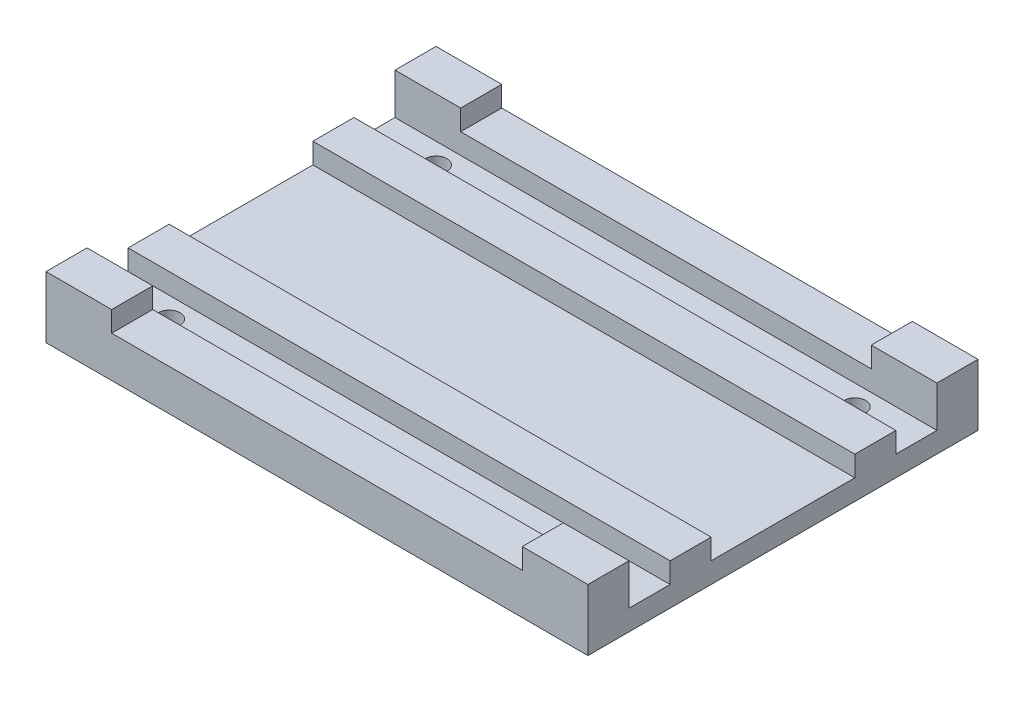
SolidWorks part; units mm, degrees
material "ABS"
ref_plane "Front Plane" through (0, 0, 0) normal (0, 0, 1) x (1, 0, 0)
ref_plane "Top Plane" through (0, 0, 0) normal (0, 1, 0) x (1, 0, 0)
ref_plane "Right Plane" through (0, 0, 0) normal (1, 0, 0) x (0, 0, -1)
sketch "Sketch1" plane through (0, 0, 0) normal (0, 1, 0) x (1, 0, 0)
  line L0 (-66, -47.5) -> (66, -47.5)
  line L1 (-66, -47.5) -> (-66, 47.5)
  line L2 (66, -47.5) -> (66, 47.5)
  line L3 (-66, 47.5) -> (66, 47.5)
  line L4 (-66, -47.5) -> (66, 47.5) construction
  line L5 (66, -47.5) -> (-66, 47.5) construction
  point P1 (0, 0)
  dimension "D1" = 95
  dimension "D2" = 132
extrude "Boss-Extrude1" add sketch "Sketch1" along normal blind 5
hole_wizard "M5 Clearance Slot1" positions "Sketch3" profile "Sketch2" size "M5" standard "ANSI Metric" slot yes end condition through all
sketch "Sketch3" plane through (0, 5, 0) normal (0, 1, 0) x (1, 0, 0)
  line L0 (-66, 47.5) -> (-66, -47.5) construction
  line L1 (66, 47.5) -> (-66, 47.5) construction
  line L2 (-51, 32.5) -> (51, 32.5) construction
  line L3 (51, 32.5) -> (51, -32.5) construction
  line L4 (51, -32.5) -> (-51, -32.5) construction
  line L5 (-51, -32.5) -> (-51, 32.5) construction
  line L7 (66, -47.5) -> (66, 47.5) construction
  line L8 (-66, -47.5) -> (66, -47.5) construction
  point P0 (-51, 32.5)
  point P2 (51, 32.5)
  point P4 (51, -32.5)
  point P6 (-51, -32.5)
  dimension "D1" = 15
  dimension "D2" = 15
  dimension "D3" = 15
  dimension "D4" = 15
sketch "Sketch2" plane through (-51, 5, -32.5) normal (1, 0, 0) x (0, 0, 1)
  line L0 (0, 0) -> (0, 5)
  line L1 (0, 5) -> (2.65, 5)
  line L2 (2.65, 5) -> (2.65, 0)
  line L5 (2.65, 0) -> (0, 0)
  line L11 (0, -6.35) -> (0, 107.95) construction
  dimension "Thru Hole Dia." = 5.3
  dimension "Thru Hole Depth" = 5
sketch "Sketch4" plane through (0, 5, 0) normal (0, 1, 0) x (1, 0, 0)
  line L0 (-66, 27.5) -> (-66, 17.5)
  line L1 (-66, 27.5) -> (66, 27.5)
  line L2 (-66, 17.5) -> (66, 17.5)
  line L3 (66, 27.5) -> (66, 17.5)
  line L4 (-66, 47.5) -> (-66, -47.5) construction
  line L5 (66, 37.5) -> (66, 47.5)
  line L6 (-66, 0) -> (66, 0) construction
  line L7 (66, -47.5) -> (66, 47.5) construction
  line L8 (-66, 32.5) -> (66, 32.5) construction
  line L9 (66, 47.5) -> (-66, 47.5) construction
  line L10 (-66, 47.5) -> (66, 47.5)
  line L11 (-66, 37.5) -> (-66, 47.5)
  line L12 (-66, 37.5) -> (66, 37.5)
  line L13 (-66, -27.5) -> (-66, -17.5)
  line L14 (66, -27.5) -> (66, -17.5)
  line L15 (-66, -17.5) -> (66, -17.5)
  line L16 (-66, -27.5) -> (66, -27.5)
  line L17 (66, -37.5) -> (66, -47.5)
  line L18 (-66, -37.5) -> (66, -37.5)
  line L19 (-66, -37.5) -> (-66, -47.5)
  line L20 (-66, -47.5) -> (66, -47.5)
  dimension "D1" = 15
  dimension "D2" = 10
  dimension "D3" = 5
extrude "Boss-Extrude2" add sketch "Sketch4" along normal blind 10
sketch "Sketch5" plane through (0, 15, 0) normal (0, 1, 0) x (1, 0, 0)
  line L0 (66, 27.5) -> (-66, 27.5) construction
  line L1 (-50, -50) -> (50, -50)
  line L2 (-50, -50) -> (-50, 50)
  line L3 (-50, 50) -> (50, 50)
  line L4 (50, -50) -> (50, 50)
  line L5 (-50, -50) -> (50, 50) construction
  line L6 (-50, 50) -> (50, -50) construction
  line L7 (-66, 17.5) -> (-50, 17.5)
  line L8 (-66, 17.5) -> (-66, 27.5)
  line L9 (-66, 27.5) -> (-50, 27.5)
  line L10 (-50, 17.5) -> (-50, 27.5)
  line L11 (66, -17.5) -> (-66, -17.5) construction
  line L12 (66, 17.5) -> (50, 17.5)
  line L13 (66, 17.5) -> (66, 27.5)
  line L14 (66, 27.5) -> (50, 27.5)
  line L15 (50, 17.5) -> (50, 27.5)
  line L16 (-66, -27.5) -> (-50, -27.5)
  line L17 (-66, -27.5) -> (-66, -17.5)
  line L18 (-66, -17.5) -> (-50, -17.5)
  line L19 (-50, -27.5) -> (-50, -17.5)
  line L20 (66, -27.5) -> (66, -17.5) construction
  line L21 (66, -27.5) -> (50, -27.5)
  line L22 (66, -27.5) -> (66, -17.5)
  line L23 (66, -17.5) -> (50, -17.5)
  line L24 (50, -27.5) -> (50, -17.5)
  line L25 (-66, -27.5) -> (66, -27.5) construction
  point P0 (0, 0)
  line M3 (66, -37.5) -> (-66, -37.5)
  line M5 (-66, -47.5) -> (66, -47.5)
  dimension "D1" = 100
  dimension "D2" = 100
extrude "Cut-Extrude1" cut sketch "Sketch5" against normal blind 5 contours L4 L3 L2 M3 | L4 L2 M5 M3 | L1 L4 L2 M5 | L18 L17 L16 L2 | L22 L23 L4 L21 | L13 L14 L4 L12 | L9 L8 L7 L2
